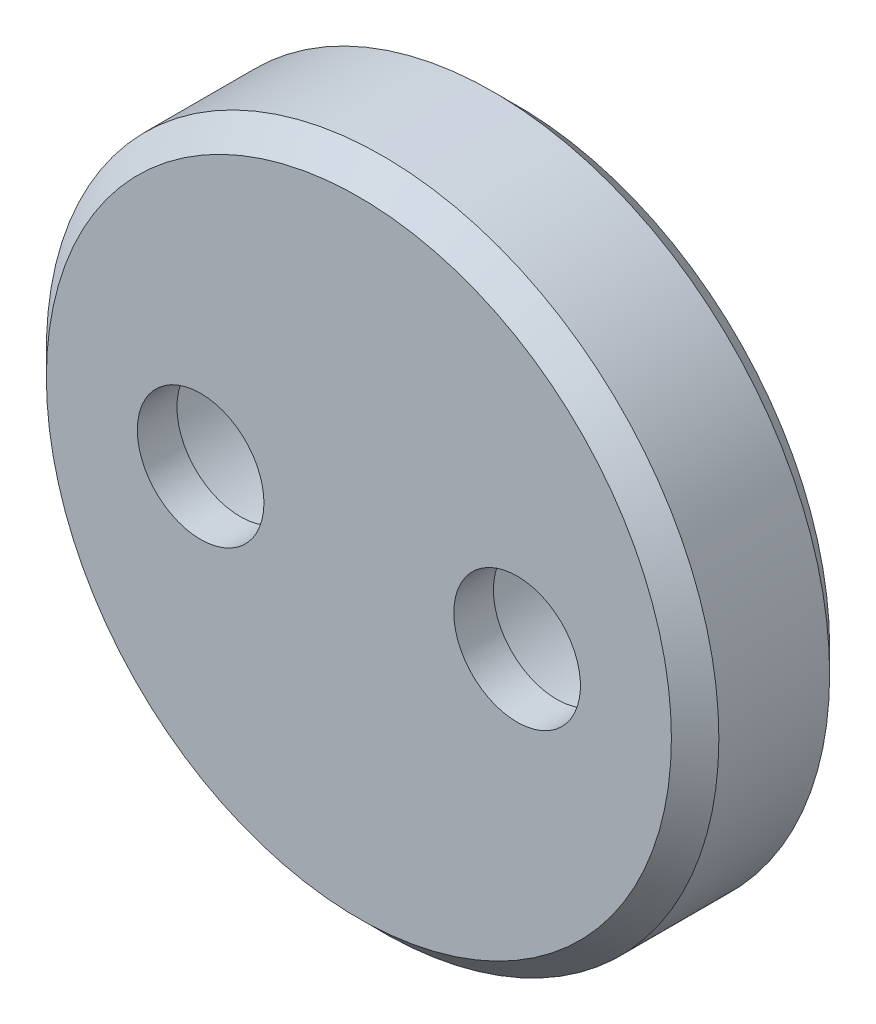
SolidWorks part; units mm, degrees
material "ABS"
ref_plane "Plan de face" through (0, 0, 0) normal (0, 0, 1) x (1, 0, 0)
ref_plane "Plan de dessus" through (0, 0, 0) normal (0, 1, 0) x (1, 0, 0)
ref_plane "Plan de droite" through (0, 0, 0) normal (1, 0, 0) x (0, 0, -1)
sketch "Esquisse1" plane through (0, 0, 0) normal (0, 0, 1) x (1, 0, 0)
  line L0 (0, 0) -> (0, 8.5) construction
  line L1 (0, 0) -> (4, 0) construction
  circle A0 centre (0, 0) radius 8.5
  circle A1 centre (-4, 0) radius 1.6
  circle A2 centre (4, 0) radius 1.6
  dimension "D1" = 3.2
  dimension "D3" = 17
  dimension "D2" = 8
extrude "Boss.-Extru.1" add sketch "Esquisse1" along normal blind 4
sketch "Esquisse3" plane through (0, 0, 0) normal (0, 0, -1) x (-1, 0, 0)
  circle A0 centre (4, 0) radius 2.9
  circle A1 centre (-4, 0) radius 2.9
  dimension "D1" = 5.8
extrude "Enlèv. mat.-Extru.1" cut sketch "Esquisse3" against normal blind 3
chamfer "Chanfrein1" distance 0.6 angle 45 2 edges at (8.5, 0, 4) (8.5, 0, 0)
